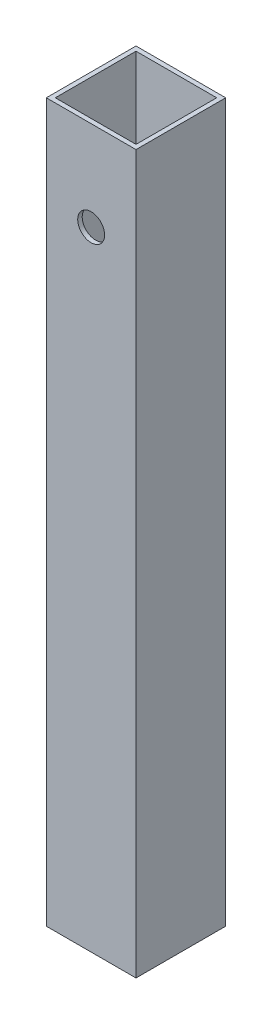
SolidWorks part; units mm, degrees
ref_plane "Front" through (0, 0, 0) normal (0, 0, 1) x (1, 0, 0)
ref_plane "Top" through (0, 0, 0) normal (0, 1, 0) x (1, 0, 0)
ref_plane "Right" through (0, 0, 0) normal (1, 0, 0) x (0, 0, -1)
sketch "草图1" plane through (0, 0, 0) normal (0, 1, 0) x (1, 0, 0)
  line L0 (-18.0928, 0) -> (21.4607, 0) construction
  line L1 (0, 24.5757) -> (0, -21.0047) construction
  line L3 (-10, 10) -> (10, 10)
  line L4 (-10, 10) -> (-10, -10)
  line L5 (-10, -10) -> (10, -10)
  line L6 (10, 10) -> (10, -10)
  line L7 (-9, 9) -> (9, 9)
  line L8 (-9, 9) -> (-9, -9)
  line L9 (-9, -9) -> (9, -9)
  line L10 (9, 9) -> (9, -9)
  dimension "D1" = 20
  dimension "D2" = 20
  dimension "D3" = 10
  dimension "D4" = 10
  dimension "D5" = 9
  dimension "D6" = 18
  dimension "D7" = 18
  dimension "D8" = 9
extrude "凸台-拉伸1" add sketch "草图1" along normal blind 140
sketch "草图2" plane through (0, 0, 0) normal (0, -1, 0) x (1, 0, 0)
  line L1 (-10, 10) -> (10, 10)
  line L2 (-10, 10) -> (-10, -10)
  line L3 (-10, -10) -> (10, -10)
  line L4 (10, 10) -> (10, -10)
extrude "凸台-拉伸2" add sketch "草图2" along normal blind 20
sketch "草图3" plane through (0, 0, 10) normal (0, 0, 1) x (1, 0, 0)
  line L0 (0, 140) -> (0, -20) construction
  line L1 (-10, 140) -> (10, 140) construction
  line L2 (10, -20) -> (-10, -20) construction
  circle A0 centre (0, 120) radius 3
  dimension "D1" = 20
extrude "切除-拉伸1" cut sketch "草图3" against normal blind 2
